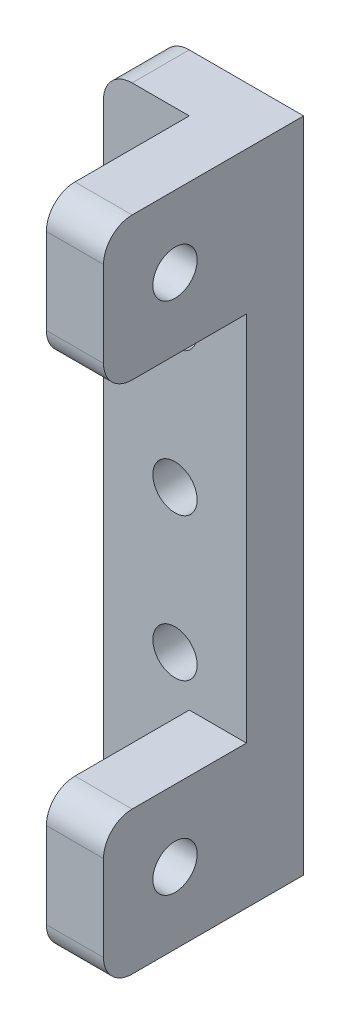
SolidWorks part; units mm, degrees
ref_plane "Front" through (0, 0, 0) normal (0, 0, 1) x (1, 0, 0)
ref_plane "Top" through (0, 0, 0) normal (0, 1, 0) x (1, 0, 0)
ref_plane "Right" through (0, 0, 0) normal (1, 0, 0) x (0, 0, -1)
sketch "Sketch1" plane through (0, 0, 0) normal (0, 0, 1) x (1, 0, 0)
  line L1 (-5, -23) -> (5, -23)
  line L2 (-5, -23) -> (-5, 23)
  line L3 (-5, 23) -> (5, 23)
  line L4 (5, -23) -> (5, 23)
  line L5 (-5, -23) -> (5, 23) construction
  line L6 (-5, 23) -> (5, -23) construction
  circle A0 centre (0, 10) radius 1.55
  circle A1 centre (0, 0) radius 1.55
  circle A2 centre (0, -10) radius 1.55
  point P0 (0, 0)
  dimension "D3" = 3.1
  dimension "D4" = 3.1
  dimension "D5" = 3.1
  dimension "D6" = 10
  dimension "D7" = 10
  dimension "D1" = 46
  dimension "D2" = 10
extrude "Boss-Extrude1" add sketch "Sketch1" along normal blind 4
sketch "Sketch2" plane through (0, 0, 4) normal (0, 0, 1) x (1, 0, 0)
  line L1 (5, 23) -> (1, 23)
  line L2 (5, 23) -> (5, 13)
  line L3 (5, 13) -> (1, 13)
  line L4 (1, 23) -> (1, 13)
  line L5 (5, 23) -> (1, 13) construction
  line L6 (5, 13) -> (1, 23) construction
  line L7 (5, -23) -> (1, -23)
  line L8 (5, -23) -> (5, -13)
  line L9 (5, -13) -> (1, -13)
  line L10 (1, -23) -> (1, -13)
  line L11 (5, -23) -> (1, -13) construction
  line L12 (5, -13) -> (1, -23) construction
  point P4 (3, 18)
  point P12 (3, -18)
  dimension "D3" = 10
  dimension "D1" = 4
  dimension "D2" = 10
extrude "Boss-Extrude2" add sketch "Sketch2" along normal blind 10
sketch "Sketch3" plane through (1, 0, 0) normal (-1, 0, 0) x (0, 0, 1)
  line L0 (14, 23) -> (4, 23) construction
  line L1 (14, 23) -> (14, 13) construction
  line L2 (14, -23) -> (4, -23) construction
  circle A0 centre (9, 18) radius 1.55
  circle A1 centre (9, -18) radius 1.55
  dimension "D1" = 3.1
  dimension "D2" = 3.1
  dimension "D3" = 5
  dimension "D4" = 5
  dimension "D5" = 5
extrude "Cut-Extrude1" cut sketch "Sketch3" against normal up to next
fillet "Fillet1" radius 2 6 edges at (3, 23, 14) (-5, 23, 2) (3, 13, 14) (-5, -23, 2) (3, -13, 14) (3, -23, 14)
